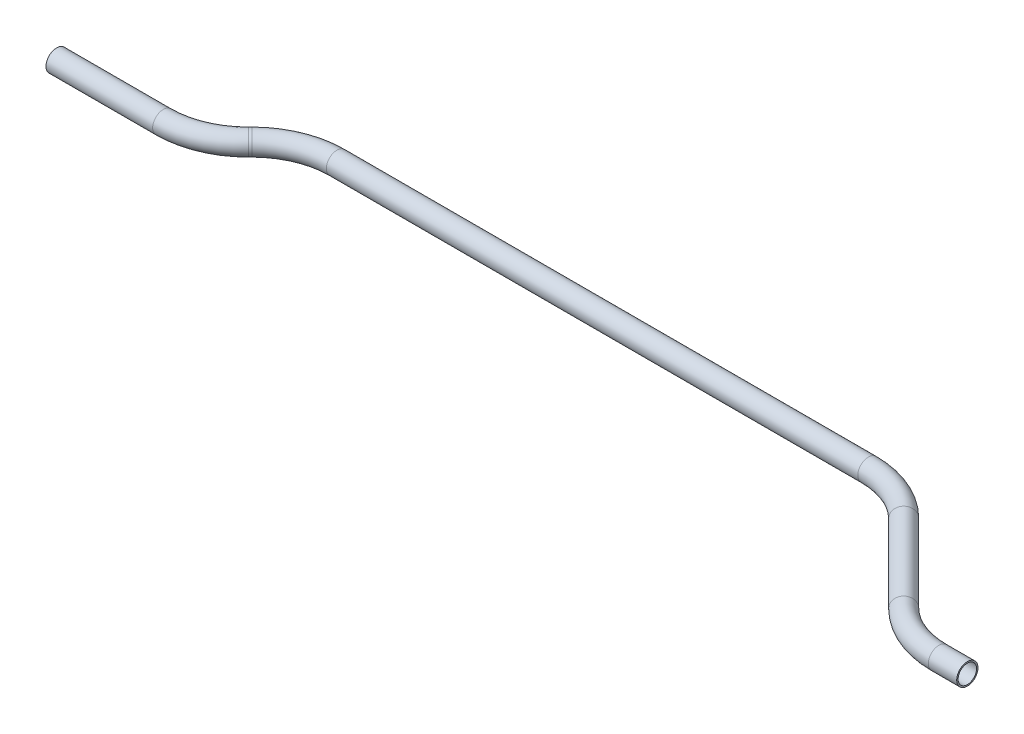
SolidWorks part; units mm, degrees
ref_plane "Front Plane" through (0, 0, 0) normal (0, 0, 1) x (1, 0, 0)
ref_plane "Top Plane" through (0, 0, 0) normal (0, 1, 0) x (1, 0, 0)
ref_plane "Right Plane" through (0, 0, 0) normal (1, 0, 0) x (0, 0, -1)
sketch "Sketch1" plane through (0, 0, 0) normal (0, 1, 0) x (1, 0, 0)
  line L0 (0, 0) -> (95.4369, 0)
  line L1 (149.3185, 22.3185) -> (150.8254, 23.8254)
  line L2 (204.7069, 46.1439) -> (680.2503, 46.1439)
  line L3 (734.1318, 23.8254) -> (803.7949, -45.8377)
  line L4 (857.6764, -68.1561) -> (883.0764, -68.1561)
  arc A0 (803.7949, -45.8377) -> (857.6764, -68.1561) centre (857.6764, 8.0439) ccw
  arc A1 (680.2503, 46.1439) -> (734.1318, 23.8254) centre (680.2503, -30.0561) cw
  arc A2 (150.8254, 23.8254) -> (204.7069, 46.1439) centre (204.7069, -30.0561) cw
  arc A3 (95.4369, 0) -> (149.3185, 22.3185) centre (95.4369, 76.2) ccw
  point P9 (826.1133, -68.1561)
  point P12 (711.8133, 46.1439)
  point P15 (173.1439, 46.1439)
  point P18 (127, 0)
  dimension "D8" = 76.2
  dimension "D1" = 127
  dimension "D2" = 135
  dimension "D3" = 25.4
  dimension "D4" = 883.0764
  dimension "D5" = 114.3
  dimension "D6" = 45
  dimension "D7" = 46.1439
ref_plane "Plane1" through (0, 0, 0) normal (1, 0, 0) x (0, 0, -1)
sketch "Sketch2" plane through (0, 0, 0) normal (1, 0, 0) x (0, 0, -1)
  circle A0 centre (0, 0) radius 9.525
  circle A1 centre (0, 0) radius 8.2804
  dimension "D1" = 19.05
  dimension "D2" = 1.2446
sweep "Sweep1" add profiles "Sketch2" path "Sketch1"
